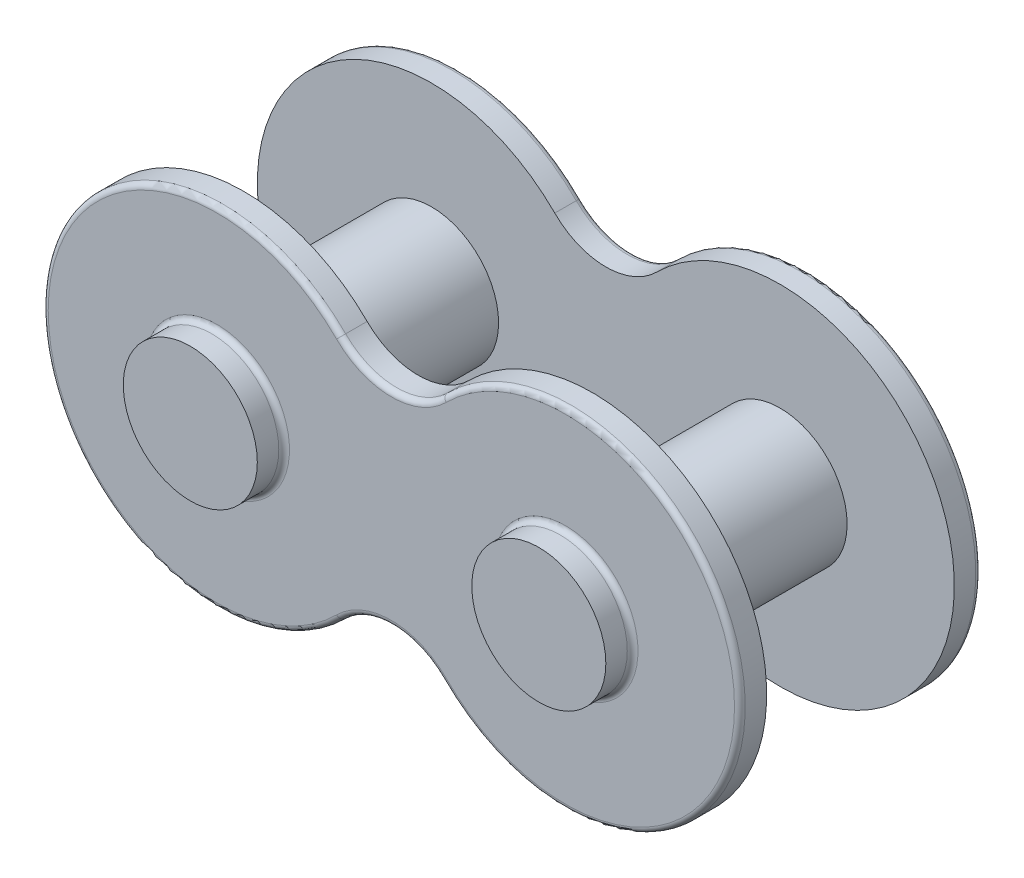
SolidWorks part; units mm, degrees
ref_plane "Alzado" through (0, 0, 0) normal (0, 0, 1) x (1, 0, 0)
ref_plane "Planta" through (0, 0, 0) normal (0, 1, 0) x (1, 0, 0)
ref_plane "Vista lateral" through (0, 0, 0) normal (1, 0, 0) x (0, 0, -1)
sketch "Croquis1" plane through (0, 0, 0) normal (0, 0, 1) x (1, 0, 0)
  line L0 (0, 9.6781) -> (0, 9.1924) construction
  line L1 (-6.5, 0) -> (6.5, 0) construction
  circle A0 centre (-6.5, 0) radius 2.5
  circle A1 centre (6.5, 0) radius 2.5
  arc A2 (-1.9038, 4.5962) -> (-1.9038, -4.5962) centre (-6.5, 0) ccw
  arc A3 (1.9038, -4.5962) -> (1.9038, 4.5962) centre (6.5, 0) ccw
  arc A4 (-1.9038, 4.5962) -> (1.9038, 4.5962) centre (0, 6.5) ccw
  arc A5 (1.9038, -4.5962) -> (-1.9038, -4.5962) centre (0, -6.5) ccw
  point P6 (0, 0)
  point P13 (0, 0)
  dimension "D2" = 5
  dimension "D4" = 5
  dimension "D1" = 13
  dimension "D3" = 13
extrude "Saliente-Extruir1" add sketch "Croquis1" along normal blind 1
sketch "Croquis2" plane through (0, 0, 0) normal (0, 0, 1) x (1, 0, 0)
  circle A0 centre (-6.5, 0) radius 2.5
  circle A1 centre (6.5, 0) radius 2.5
  dimension "D1" = 5
  dimension "D2" = 5
extrude "Saliente-Extruir2" add sketch "Croquis2" along normal blind 10 and the other way blind 1
ref_plane "Plano2" through (0, 0, 4.5) normal (0, 0, -1) x (-1, 0, 0)
mirror "Simetría1" about plane through (0, 0, 4.5) normal (0, 0, -1) of "Saliente-Extruir1"
fillet "Redondeo1" radius 0.2 12 edges at (9, 0, 0) (-4, 0, 0) (-4, 0, 9) (9, 0, 9) (13, 0, 0) (0, 3.8076, 0) (-13, 0, 0) (0, -3.8076, 0) (-13, 0, 9) (0, 3.8076, 9) (13, 0, 9) (0, -3.8076, 9)
